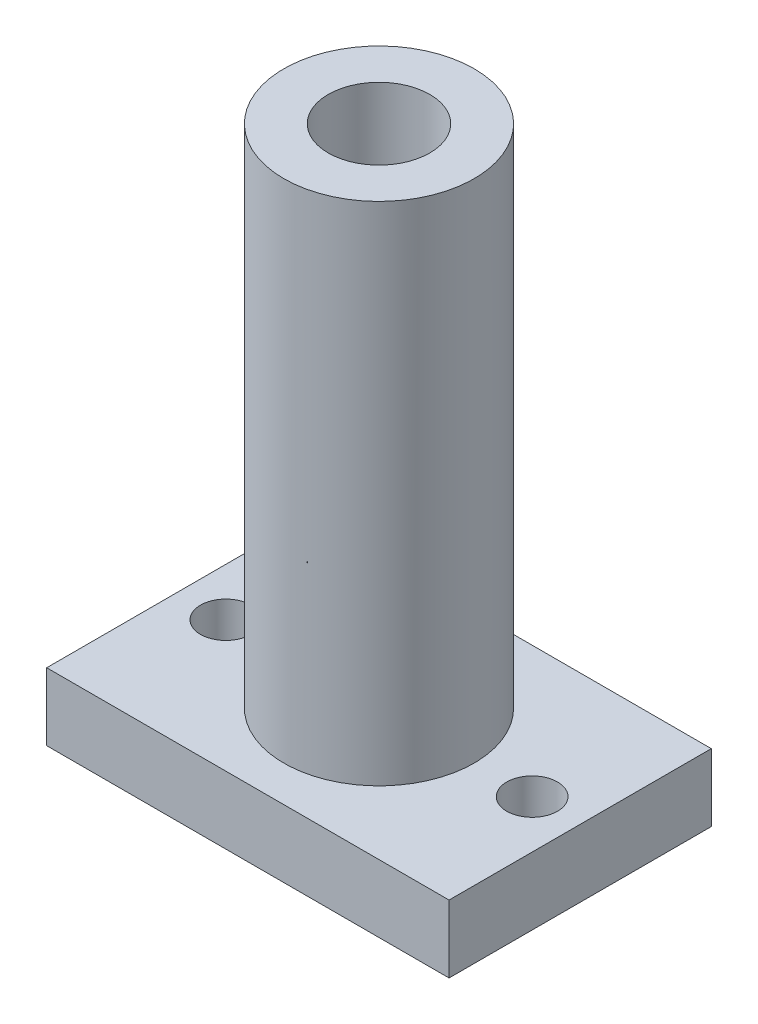
SolidWorks part; units mm, degrees
ref_plane "Front Plane" through (0, 0, 0) normal (0, 0, 1) x (1, 0, 0)
ref_plane "Top Plane" through (0, 0, 0) normal (0, 1, 0) x (1, 0, 0)
ref_plane "Right Plane" through (0, 0, 0) normal (1, 0, 0) x (0, 0, -1)
sketch "Sketch1" plane through (0, 0, 0) normal (0, 1, 0) x (1, 0, 0)
  line L1 (0, 0) -> (31.7, 0)
  line L2 (0, 0) -> (0, 20.66)
  line L3 (0, 20.66) -> (31.7, 20.66)
  line L4 (31.7, 0) -> (31.7, 20.66)
  dimension "D1" = 20.66
  dimension "D2" = 31.7
extrude "Boss-Extrude1" add sketch "Sketch1" along normal blind 5.32
sketch "Sketch2" plane through (0, 5.32, 0) normal (0, 1, 0) x (1, 0, 0)
  line L0 (0, 10.33) -> (31.7, 10.33) construction
  line L1 (0, 20.66) -> (0, 0) construction
  line L2 (31.7, 0) -> (31.7, 20.66) construction
  line L3 (3.785, 10.33) -> (0, 10.33) construction
  line L4 (27.915, 10.33) -> (31.7, 10.33) construction
  circle A0 centre (3.785, 10.33) radius 2
  circle A1 centre (27.915, 10.33) radius 2
  dimension "D2" = 4
  dimension "D1" = 24.13
extrude "Cut-Extrude1" cut sketch "Sketch2" against normal blind 5.32
sketch "Sketch3" plane through (0, 5.32, 0) normal (0, 1, 0) x (1, 0, 0)
  line L0 (0, 10.33) -> (31.7, 10.33) construction
  line L1 (0, 20.66) -> (0, 0) construction
  line L2 (31.7, 0) -> (31.7, 20.66) construction
  circle A0 centre (15.85, 10.33) radius 7.5
  circle A1 centre (15.85, 10.33) radius 4
  dimension "D1" = 15
  dimension "D2" = 8
extrude "Boss-Extrude2" add sketch "Sketch3" along normal blind 39.88
sketch "Sketch4" plane through (0, 5.32, 0) normal (0, 1, 0) x (1, 0, 0)
  circle A0 centre (15.85, 10.33) radius 4
  dimension "D1" = 8
extrude "Cut-Extrude2" cut sketch "Sketch4" against normal blind 39.88
